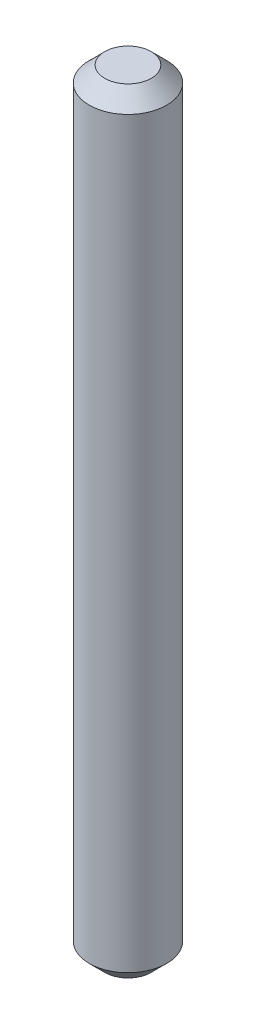
SolidWorks part; units mm, degrees
material "Stainless Steel (ferritic)"
ref_plane "Front Plane" through (0, 0, 0) normal (0, 0, 1) x (1, 0, 0)
ref_plane "Top Plane" through (0, 0, 0) normal (0, 1, 0) x (1, 0, 0)
ref_plane "Right Plane" through (0, 0, 0) normal (1, 0, 0) x (0, 0, -1)
sketch "Sketch1" plane through (0, 0, 0) normal (0, 1, 0) x (1, 0, 0)
  circle A0 centre (0, 0) radius 2.5
  dimension "D1" = 5
extrude "Boss-Extrude1" add sketch "Sketch1" along normal blind 50
chamfer "Chamfer1" distance 1 angle 45 2 edges at (0, 0, 2.5) (0, 50, 2.5)
ref_plane "Plane1" through (0, 25, 0) normal (0, 1, 0) x (1, 0, 0)
